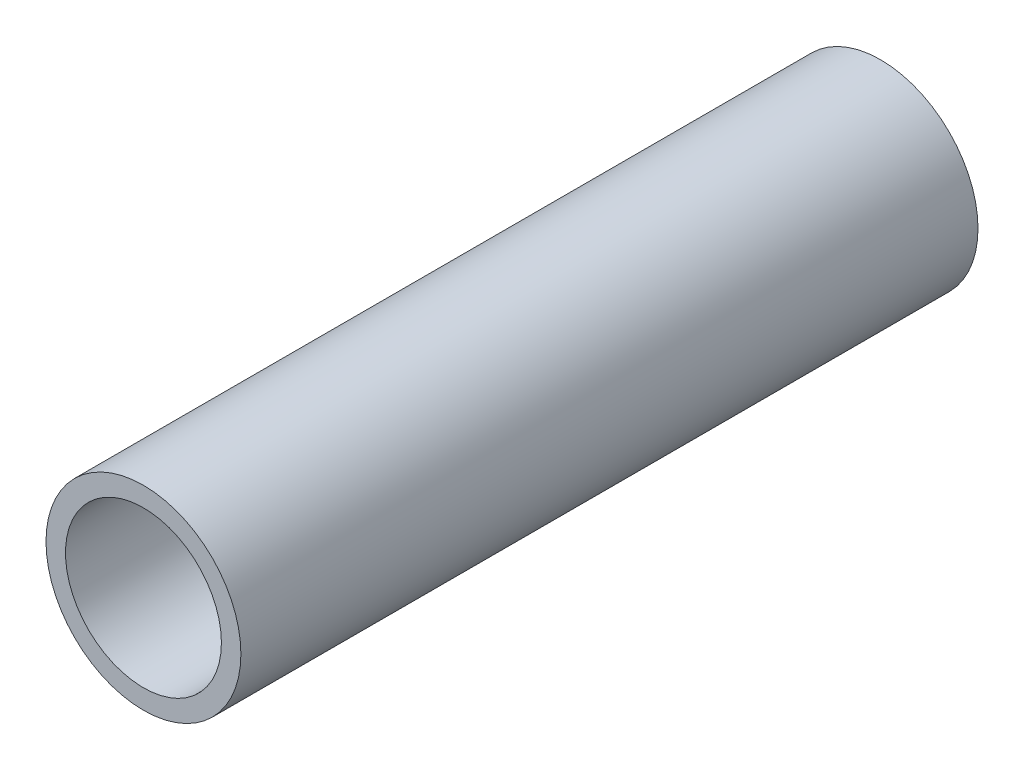
SolidWorks part; units mm, degrees
ref_plane "Front Plane" through (0, 0, 0) normal (0, 0, 1) x (1, 0, 0)
ref_plane "Top Plane" through (0, 0, 0) normal (0, 1, 0) x (1, 0, 0)
ref_plane "Right Plane" through (0, 0, 0) normal (1, 0, 0) x (0, 0, -1)
sketch "Sketch1" plane through (0, 0, 0) normal (0, 0, 1) x (1, 0, 0)
  circle A0 centre (0, 0) radius 1.25
  circle A1 centre (0, 0) radius 1
  dimension "D1" = 2
  dimension "D2" = 2.5
extrude "Boss-Extrude1" add sketch "Sketch1" along normal blind 9.455
equation "\"D1@Boss-Extrude1\"= ( \"D8@Sketch2@indexMIP.SLDPRT\" - \"D6@Sketch2@indexMIP.SLDPRT\" ) * 2'Tube MIP Length"
